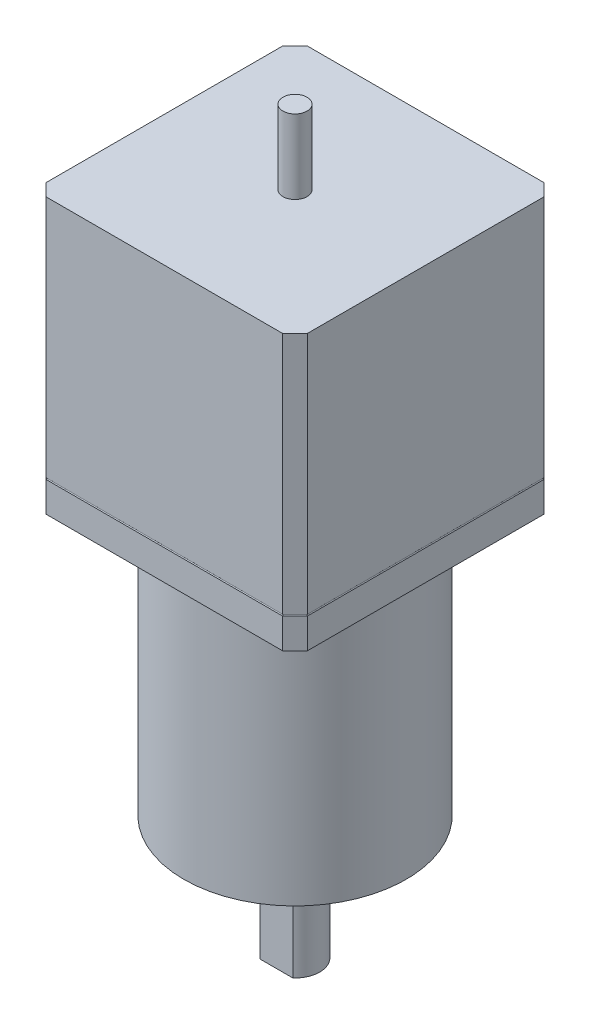
SolidWorks part; units mm, degrees
ref_plane "Front Plane" through (0, 0, 0) normal (0, 0, 1) x (1, 0, 0)
ref_plane "Top Plane" through (0, 0, 0) normal (0, 1, 0) x (1, 0, 0)
ref_plane "Right Plane" through (0, 0, 0) normal (1, 0, 0) x (0, 0, -1)
sketch "Sketch1" plane through (0, 0, 0) normal (0, 1, 0) x (1, 0, 0)
  line L1 (0, 0) -> (-42.3, 0)
  line L2 (0, 0) -> (0, -42.3)
  line L3 (0, -42.3) -> (-42.3, -42.3)
  line L4 (-42.3, 0) -> (-42.3, -42.3)
  dimension "D1" = 42.3
  dimension "D2" = 42.3
extrude "Boss-Extrude1" add sketch "Sketch1" along normal blind 44.5
chamfer "Chamfer1" distance 2 angle 45 4 edges at (-42.3, 22.25, 42.3) (0, 22.25, 42.3) (0, 22.25, 0) (-42.3, 22.25, 0)
sketch "Sketch3" plane through (0, 44.5, 0) normal (0, 1, 0) x (1, 0, 0)
  line L0 (-21.15, 0) -> (-21.15, -42.3) construction
  line L1 (-2, 0) -> (-40.3, 0) construction
  line L2 (-40.3, -42.3) -> (-2, -42.3) construction
  circle A0 centre (-21.15, -21.15) radius 1.95
  dimension "D1" = 3.9
extrude "Boss-Extrude2" add sketch "Sketch3" along normal blind 12
sketch "Sketch4" plane through (0, 0, 0) normal (0, -1, 0) x (1, 0, 0)
  line L0 (-21.15, 42.3) -> (-21.15, 0) construction
  line L1 (-40.3, 42.3) -> (-2, 42.3) construction
  line L2 (-2, 0) -> (-40.3, 0) construction
  circle A0 centre (-21.15, 21.15) radius 18
  dimension "D1" = 36
extrude "Boss-Extrude3" add sketch "Sketch4" along normal blind 43.2
ref_plane "Plane1" through (0, 5, 0) normal (0, -1, 0) x (-1, 0, 0)
sketch "Sketch5" plane through (0, 5, 0) normal (0, -1, 0) x (-1, 0, 0)
  line L0 (2, 0) -> (0, -2) construction
  line L1 (0, -40.3) -> (0, -2) construction
  line L2 (0, -40.3) -> (2, -42.3) construction
  line L3 (40.3, -42.3) -> (2, -42.3) construction
  line L4 (40.3, -42.3) -> (42.3, -40.3) construction
  line L5 (42.3, -2) -> (42.3, -40.3) construction
  line L6 (42.3, -2) -> (40.3, 0) construction
  line L7 (2, 0) -> (40.3, 0) construction
  line L8 (2, 0) -> (0, -2)
  line L9 (0, -40.3) -> (0, -2)
  line L10 (0, -40.3) -> (2, -42.3)
  line L11 (40.3, -42.3) -> (2, -42.3)
  line L12 (40.3, -42.3) -> (42.3, -40.3)
  line L13 (42.3, -2) -> (42.3, -40.3)
  line L14 (42.3, -2) -> (40.3, 0)
  line L15 (2, 0) -> (40.3, 0)
sketch "Sketch6" plane through (0, 0, 0) normal (1, 0, 0) x (0, 0, -1)
  line L0 (-40.3, 5) -> (-42.3, 5) construction
  line L1 (-40.3, 44.5) -> (-40.3, 0) construction
  circle A0 centre (-40.3, 5) radius 0.125
  dimension "D1" = 0.25
sweep "Cut-Sweep2" cut profiles "Sketch6" path "Sketch5"
sketch "Sketch7" plane through (0, -43.2, 0) normal (0, -1, 0) x (1, 0, 0)
  line L0 (-21.15, 21.15) -> (-21.15, 39.15) construction
  circle A0 centre (-21.15, 21.15) radius 18 construction
  circle A1 centre (-21.15, 21.15) radius 11
  dimension "D1" = 22
extrude "Boss-Extrude4" add sketch "Sketch7" along normal blind 2 contours A1
sketch "Sketch9" plane through (0, -45.2, 0) normal (0, -1, 0) x (1, 0, 0)
  circle A0 centre (-21.15, 21.15) radius 4
  dimension "D1" = 8
extrude "Boss-Extrude5" add sketch "Sketch9" along normal blind 18
sketch "Sketch10" plane through (0, -63.2, 0) normal (0, -1, 0) x (1, 0, 0)
  line L0 (-23.7958, 24.15) -> (-18.5042, 24.15)
  line L1 (-18.5042, 24.15) -> (-18.5042, 27.15)
  line L2 (-18.5042, 27.15) -> (-23.7958, 27.15)
  line L3 (-23.7958, 27.15) -> (-23.7958, 24.15)
  line L4 (-21.15, 24.15) -> (-21.15, 17.15) construction
  circle A0 centre (-21.15, 21.15) radius 4 construction
  dimension "D1" = 7
  dimension "D2" = 3
extrude "Cut-Extrude1" cut sketch "Sketch10" against normal blind 15
sketch "Sketch11" plane through (0, -43.2, 0) normal (0, -1, 0) x (1, 0, 0)
  line L0 (-21.15, 35.15) -> (-21.15, 21.15) construction
  line L1 (-21.15, 21.15) -> (-11.2505, 31.0495) construction
  circle A0 centre (-21.15, 21.15) radius 14 construction
  dimension "D1" = 28
  dimension "D2" = 45
hole_wizard "M3 Clearance Hole1" positions "Sketch12" profile "Sketch13" hole size "M3" standard "ANSI Metric"
sketch "Sketch12" plane through (0, -43.2, 0) normal (0, -1, 0) x (-1, 0, 0)
  point P0 (11.2505, -31.0495)
sketch "Sketch13" plane through (-11.2505, -43.2, 31.0495) normal (1, 0, 0) x (0, 0, -1)
  line L0 (0, 0) -> (0, 21.0215)
  line L1 (0, 21.0215) -> (1.7, 20)
  line L2 (1.7, 20) -> (1.7, 0.025)
  line L3 (1.7, 0.025) -> (1.725, 0)
  line L5 (1.725, 0) -> (0, 0)
  line L6 (-1.7, 0.025) -> (-1.725, 0) construction
  line L10 (0, 21.0215) -> (-1.7, 20) construction
  line L11 (0, -6.35) -> (0, 107.95) construction
  dimension "Hole Dia." = 3.4
  dimension "Hole Depth" = 20
  dimension "Near C'Sink Dia." = 3.45
  dimension "Near C'Sink Angle" = 90
  dimension "Drill Angle" = 118
pattern_circular "CirPattern1" count 4 over 360 about axis through (-21.15, 0, 21.15) along (0, 1, 0) of "M3 Clearance Hole1"
